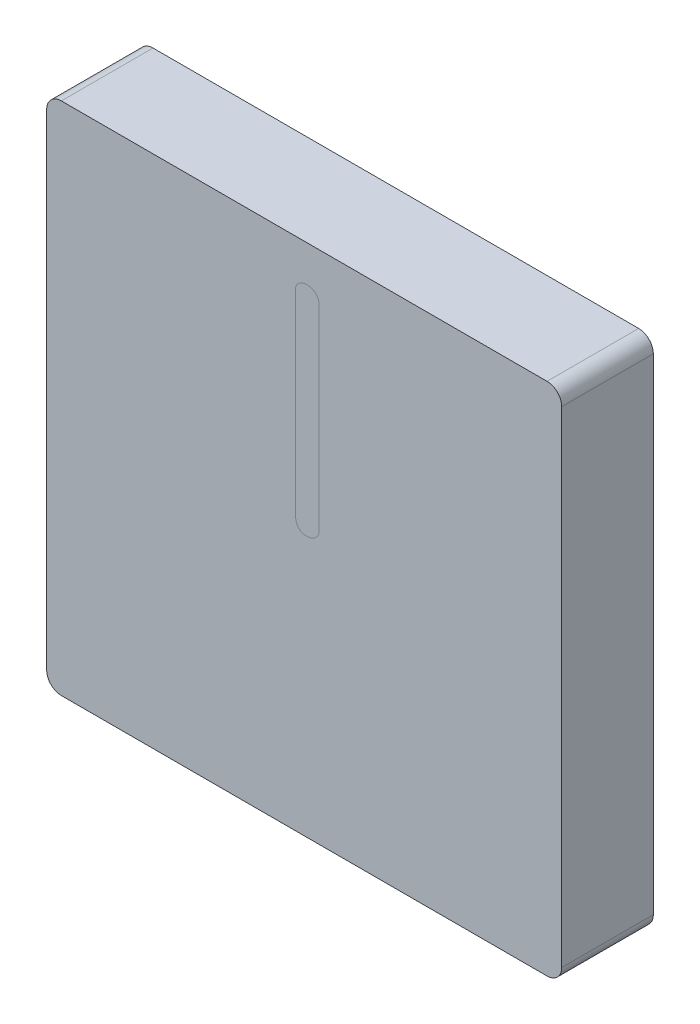
SolidWorks part; units mm, degrees
material "Nylon 101"
ref_plane "Front Plane" through (0, 0, 0) normal (0, 0, 1) x (1, 0, 0)
ref_plane "Top Plane" through (0, 0, 0) normal (0, 1, 0) x (1, 0, 0)
ref_plane "Right Plane" through (0, 0, 0) normal (1, 0, 0) x (0, 0, -1)
sketch "Sketch1" plane through (0, 0, 0) normal (0, 0, 1) x (1, 0, 0)
  line L0 (4.207, 4.715) -> (-4.207, 4.715) construction
  line L1 (4.715, -4.207) -> (4.715, 4.207) construction
  line L2 (-4.207, -4.715) -> (4.207, -4.715) construction
  line L3 (-4.715, 4.207) -> (-4.715, -4.207) construction
  line L4 (4.207, 4.715) -> (-4.207, 4.715) construction
  line L5 (4.715, -4.207) -> (4.715, 4.207) construction
  line L6 (-4.207, -4.715) -> (4.207, -4.715) construction
  line L7 (-4.715, 4.207) -> (-4.715, -4.207) construction
  line L8 (4.207, 4.461) -> (-4.207, 4.461)
  line L9 (-4.461, 4.207) -> (-4.461, -4.207)
  line L10 (-4.207, -4.461) -> (4.207, -4.461)
  line L11 (4.461, -4.207) -> (4.461, 4.207)
  arc A0 (4.715, 4.207) -> (4.207, 4.715) centre (4.207, 4.207) ccw construction
  arc A1 (4.207, -4.715) -> (4.715, -4.207) centre (4.207, -4.207) ccw construction
  arc A2 (-4.715, -4.207) -> (-4.207, -4.715) centre (-4.207, -4.207) ccw construction
  arc A3 (-4.207, 4.715) -> (-4.715, 4.207) centre (-4.207, 4.207) ccw construction
  arc A4 (4.715, 4.207) -> (4.207, 4.715) centre (4.207, 4.207) ccw construction
  arc A5 (4.207, -4.715) -> (4.715, -4.207) centre (4.207, -4.207) ccw construction
  arc A6 (-4.715, -4.207) -> (-4.207, -4.715) centre (-4.207, -4.207) ccw construction
  arc A7 (-4.207, 4.715) -> (-4.715, 4.207) centre (-4.207, 4.207) ccw construction
  arc A8 (-4.207, 4.461) -> (-4.461, 4.207) centre (-4.207, 4.207) ccw
  arc A9 (-4.461, -4.207) -> (-4.207, -4.461) centre (-4.207, -4.207) ccw
  arc A10 (4.207, -4.461) -> (4.461, -4.207) centre (4.207, -4.207) ccw
  arc A11 (4.461, 4.207) -> (4.207, 4.461) centre (4.207, 4.207) ccw
  dimension "D1" = 0.254
extrude "Boss-Extrude1" add sketch "Sketch1" along normal blind 1.5875
sketch "Sketch2" plane through (0, 0, 1.5875) normal (0, 0, 1) x (1, 0, 0)
  line L0 (4.461, 3.8355) -> (-4.461, 3.8355) construction
  line L1 (4.461, -4.207) -> (4.461, 4.207) construction
  line L2 (-4.461, 4.207) -> (-4.461, -4.207) construction
  text T0 "1" font "GordonURWMed" height in points 16
sketch "Sketch4" plane through (0, 0, 1.5875) normal (0, 0, 1) x (1, 0, 0)
  line L0 (4.461, -0.7785) -> (-4.461, -0.7785) construction
  line L1 (4.461, -4.207) -> (4.461, 4.207) construction
  line L2 (-4.461, 4.207) -> (-4.461, -4.207) construction
  text T0 "N" font "GordonURWMed" height in points 12
wrap "Direction" [suppressed] sketch "Sketch4" source sketch "Sketch4"
split line "Number"
sketch "Sketch5" [suppressed] plane through (0, 0, 1.5875) normal (0, 0, 1) x (1, 0, 0)
  line L0 (4.461, 0) -> (-4.461, 0) construction
  line L1 (4.461, -4.207) -> (4.461, 4.207) construction
  line L2 (-4.461, 4.207) -> (-4.461, -4.207) construction
  line L3 (4.461, 1.651) -> (-4.461, 1.651) construction
  text T0 "CLR" font "GordonURWMed" height in points 14
  dimension "D1" = 1.651
wrap "CLR" [suppressed] sketch "Sketch5" source sketch "Sketch5"
sketch "Sketch6" [suppressed] plane through (0, 0, 1.5875) normal (0, 0, 1) x (1, 0, 0)
  line L0 (4.461, 0) -> (-4.461, 0) construction
  line L4 (4.461, 1.651) -> (-4.461, 1.651) construction
  text T0 "ENT" font "GordonURWCon" height in points 16
  dimension "D1" = 1.651
wrap "ENT" [suppressed] sketch "Sketch6" source sketch "Sketch6"
sketch "Sketch8" plane through (0, 0, 1.5875) normal (0, 0, 1) x (1, 0, 0)
  line L0 (4.461, 3.302) -> (-4.461, 3.302) construction
  line L3 (4.461, 0) -> (-4.461, 0) construction
  line L4 (4.461, -0.508) -> (-4.461, -0.508) construction
  text T0 "EM" font "GordonURWCon" height in points 14
  text T1 "CON" font "GordonURWCon" height in points 14
  point P13 (0, 0)
  dimension "D1" = 3.302
  dimension "D2" = 0.508
wrap "EMCON" [suppressed] sketch "Sketch8" source sketch "Sketch8"
sketch "Sketch9" [suppressed] plane through (0, 0, 0) normal (0, 0, 1) x (1, 0, 0)
  line L0 (4.461, 3.302) -> (-4.461, 3.302) construction
  line L3 (4.461, 0) -> (-4.461, 0) construction
  line L4 (4.461, -0.508) -> (-4.461, -0.508) construction
  text T0 "ON" font "GordonURWCon" height in points 14
  text T1 "OFF" font "GordonURWCon" height in points 14
  point P13 (0, 0)
  dimension "D1" = 3.302
  dimension "D2" = 0.508
wrap "ON-OFF" [suppressed] sketch "Sketch9" source sketch "Sketch9" thickness 0.0762 parameters "D1"=0.0762
sketch "Sketch10" [suppressed] plane through (0, 0, 0) normal (0, 0, 1) x (1, 0, 0)
  line L0 (4.461, 0) -> (-4.461, 0) construction
  line L4 (4.461, 1.651) -> (-4.461, 1.651) construction
  text T0 "IFF" font "GordonURWCon" height in points 16
  dimension "D1" = 1.651
wrap "LEGEND" [suppressed] sketch "Sketch10" source sketch "Sketch10" thickness 0.0762 parameters "D1"=0.0762
sketch "Sketch11" [suppressed] plane through (0, 0, 1.5875) normal (0, 0, 1) x (1, 0, 0)
  spline S0 degree 3 poles (0.4333, 2.1341) (0.15, 2.1032) (-0.1198, 2.088) (-0.4121, 2.1993) (-0.5959, 2.4579) (-0.6685, 2.7897) (-0.5423, 3.1163) (-0.3233, 3.3286) (-0.0755, 3.3609) (0.1283, 3.3738) (0.3391, 3.3596) (0.5236, 3.2792) (0.6786, 3.1258) (0.7786, 2.9088) (0.8035, 2.6123) (0.682, 2.313) (0.4333, 2.1341) (0.15, 2.1032) (-0.1198, 2.088) knots -0.201217 -0.119698 -0.046549 0 0.077824 0.141317 0.20865 0.291476 0.367822 0.445307 0.489891 0.538926 0.589041 0.636005 0.676198 0.739165 0.798783 0.880302 0.953451 1 1.077824 1.141317 1.20865 only from (0.1949, 2.1094) to (0.1949, 2.1094)
split line "Split Line1" [suppressed]
